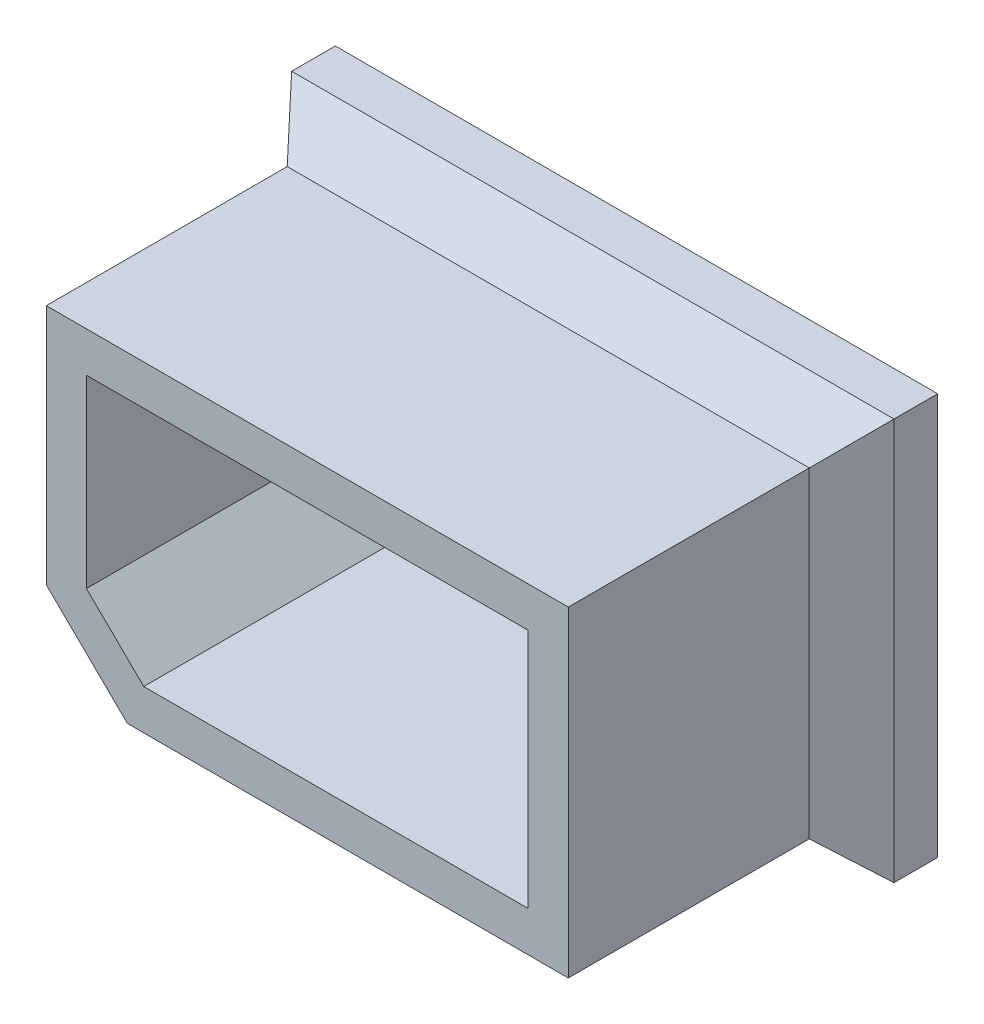
SolidWorks part; units mm, degrees
ref_plane "Front Plane" through (0, 0, 0) normal (0, 0, 1) x (1, 0, 0)
ref_plane "Top Plane" through (0, 0, 0) normal (0, 1, 0) x (1, 0, 0)
ref_plane "Right Plane" through (0, 0, 0) normal (1, 0, 0) x (0, 0, -1)
sketch "Sketch1" plane through (0, 0, 0) normal (0, 0, 1) x (1, 0, 0)
  line L1 (0, 50.8) -> (82.55, 50.8)
  line L2 (82.55, 50.8) -> (82.55, 0)
  line L6 (6.35, 44.45) -> (76.2, 44.45)
  line L7 (76.2, 44.45) -> (76.2, 6.35)
  line L10 (76.2, 6.35) -> (15.4196, 6.35)
  line L11 (15.4196, 6.35) -> (6.35, 15.24)
  line L12 (6.35, 15.24) -> (6.35, 44.45)
  line L13 (0, 50.8) -> (0, 12.5725)
  line L14 (0, 12.5725) -> (12.8265, 0)
  line L15 (12.8265, 0) -> (82.55, 0)
  dimension "D1" = 6.35
  dimension "D2" = 82.55
  dimension "D3" = 69.85
  dimension "D4" = 6.35
  dimension "D5" = 6.35
  dimension "D6" = 6.35
  dimension "D7" = 50.8
  dimension "D8" = 12.7
  dimension "D9" = 29.21
extrude "Boss-Extrude1" add sketch "Sketch1" along normal blind 38.1
sketch "Sketch2" plane through (0, 0, 0) normal (0, 0, -1) x (-1, 0, 0)
  line L0 (-88.9, 57.15) -> (-88.9, -6.35)
  line L1 (-88.9, -6.35) -> (6.35, -6.35)
  line L2 (6.35, -6.35) -> (6.35, 57.15)
  line L3 (6.35, 57.15) -> (-88.9, 57.15)
  line L4 (-82.55, 0) -> (-82.55, 50.8) construction
  line L5 (-82.55, 50.8) -> (0, 50.8) construction
  line L17 (-6.35, 44.45) -> (-6.35, 15.24)
  line L18 (-6.35, 15.24) -> (-15.4196, 6.35)
  line L19 (-15.4196, 6.35) -> (-76.2, 6.35)
  line L20 (-76.2, 6.35) -> (-76.2, 44.45)
  line L21 (-76.2, 44.45) -> (-6.35, 44.45)
  dimension "D1" = 63.5
  dimension "D2" = 95.25
  dimension "D3" = 6.35
  dimension "D4" = 6.35
extrude "Boss-Extrude2" add sketch "Sketch2" along normal blind 12.7 separate body
chamfer "Chamfer1" distance 6.35 angle 48 4 edges at (41.275, 57.15, 0) (88.9, 25.4, 0) (41.275, -6.35, 0) (-6.35, 25.4, 0)
sketch "Sketch3" plane through (0, 0, -12.7) normal (0, 0, -1) x (-1, 0, 0)
  line L0 (6.35, 25.4) -> (-88.9, 25.4) construction
  line L1 (6.35, -6.35) -> (6.35, 57.15) construction
  line L2 (-88.9, 57.15) -> (-88.9, -6.35) construction
  line L3 (-41.275, -6.35) -> (-41.275, 57.15) construction
  line L4 (-88.9, -6.35) -> (6.35, -6.35) construction
  line L5 (6.35, 57.15) -> (-88.9, 57.15) construction
  line L7 (6.35, 57.15) -> (-88.9, 57.15)
  line L8 (6.35, 57.15) -> (6.35, -6.35)
  line L9 (6.35, -6.35) -> (-88.9, -6.35)
  line L10 (-88.9, 57.15) -> (-88.9, -6.35)
  line L11 (6.35, 57.15) -> (-88.9, -6.35) construction
  line L12 (6.35, -6.35) -> (-88.9, 57.15) construction
  circle A0 centre (-41.275, 25.4) radius 9.906
  dimension "D1" = 19.812
extrude "Boss-Extrude3" add sketch "Sketch3" along normal blind 1.27
